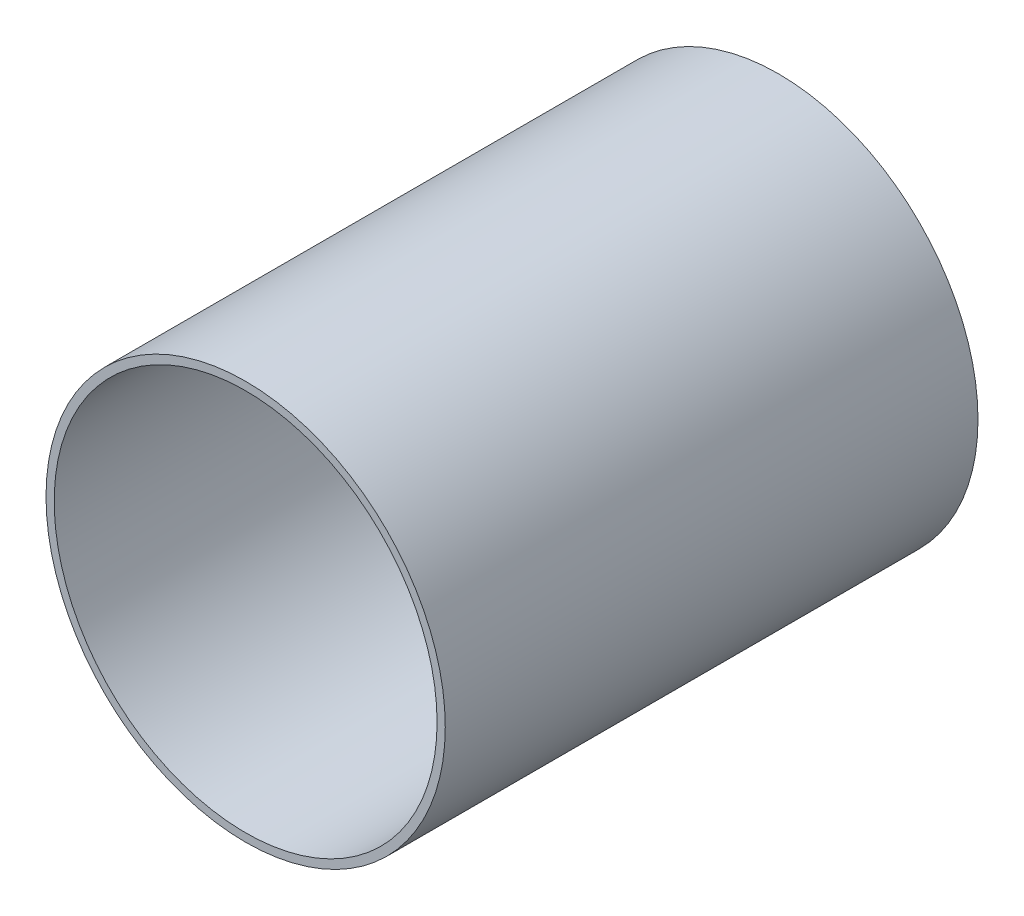
SolidWorks part; units mm, degrees
ref_plane "Front Plane" through (0, 0, 0) normal (0, 0, 1) x (1, 0, 0)
ref_plane "Top Plane" through (0, 0, 0) normal (0, 1, 0) x (1, 0, 0)
ref_plane "Right Plane" through (0, 0, 0) normal (1, 0, 0) x (0, 0, -1)
sketch "Sketch1" plane through (0, 0, 0) normal (0, 0, 1) x (1, 0, 0)
  circle A0 centre (0, 0) radius 38.0746
  circle A1 centre (0, 0) radius 36.5125
  dimension "D1" = 73.025
  dimension "D2" = 76.1492
extrude "Boss-Extrude1" add sketch "Sketch1" along normal mid plane 101.6
equation "\"AIRFRAME_OD\"= 3.091in"
equation "\"AIRFRAME_ID\"= 3.00in"
equation "\"FLAT_T\"= 0.125in"
equation "\"NOSE_EXP_L\"= 3.5in"
equation "\"NOSE_SHOULDER_L\"= 5in"
equation "\"MAIN_L\"= 30in"
equation "\"RECO_COUP_L\"= 6in"
equation "\"RECO_SWITCH_L\"= 1.5in"
equation "\"DROGUE_L\"= 14in"
equation "\"ATS_FORE_COUP_L\"= 4in"
equation "\"ATS_AFT_COUP_L\"= 2.5in"
equation "\"LOWER_L\"= 16in"
equation "\"FIN_N\"= 4"
equation "\"CR_AFT_X\"= 0.5in"
equation "\"CR_FORE_X\"= 6in"
equation "\"D1@Sketch1\"=\"COUPLER_ID\""
equation "\"D2@Sketch1\"=\"COUPLER_OD\""
equation "\"D1@Boss-Extrude1\"=\"ATS_FORE_COUP_L\""
equation "\"FIN_ROOT\"= 5in"
equation "\"FIN_X\"= 0.75in"
equation "\"MOTOR_OD\"= 2.25in"
equation "\"MOTOR_ID\"= 2.126in"
equation "\"COUPLER_OD\"= 2.998in"
equation "\"COUPLER_ID\"= 2.875in"
